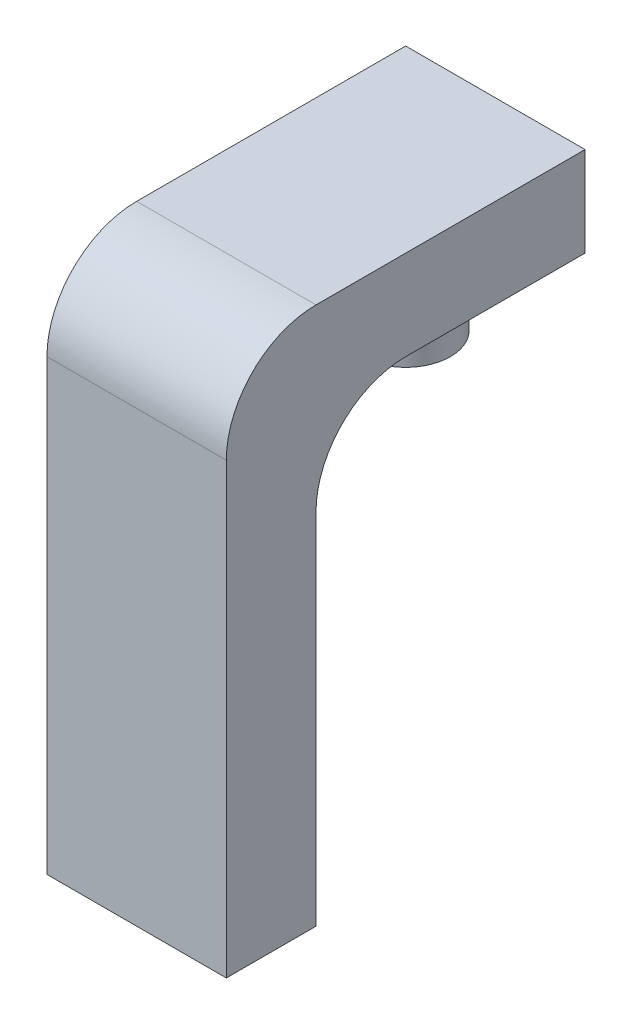
SolidWorks part; units mm, degrees
ref_plane "Alzado" through (0, 0, 0) normal (0, 0, 1) x (1, 0, 0)
ref_plane "Planta" through (0, 0, 0) normal (0, 1, 0) x (1, 0, 0)
ref_plane "Vista lateral" through (0, 0, 0) normal (1, 0, 0) x (0, 0, -1)
sketch "Croquis1" plane through (0, 0, 0) normal (1, 0, 0) x (0, 0, -1)
  line L0 (0, 0) -> (25.4, 0)
  line L1 (0, 0) -> (0, 127)
  line L2 (25.4, 152.4) -> (101.6, 152.4)
  line L3 (101.6, 152.4) -> (101.6, 127)
  line L4 (101.6, 127) -> (50.8, 127)
  line L5 (25.4, 101.6) -> (25.4, 0)
  arc A0 (0, 127) -> (25.4, 152.4) centre (25.4, 127) cw
  arc A1 (50.8, 127) -> (25.4, 101.6) centre (50.8, 101.6) ccw
  dimension "D1" = 25.4
  dimension "D2" = 25.4
  dimension "D3" = 127
  dimension "D4" = 101.6
  dimension "D5" = 76.2
extrude "Saliente-Extruir1" add sketch "Croquis1" along normal blind 50.8
sketch "Croquis2" plane through (0, 127, 0) normal (0, -1, 0) x (1, 0, 0)
  line L0 (25.4, -50.8) -> (25.4, -101.6) construction
  line L1 (50.8, -50.8) -> (0, -50.8) construction
  line L2 (50.8, -101.6) -> (0, -101.6) construction
  line L3 (0, -76.2) -> (50.8, -76.2) construction
  line L4 (0, -50.8) -> (0, -101.6) construction
  line L5 (50.8, -50.8) -> (50.8, -101.6) construction
  circle A0 centre (25.4, -76.2) radius 12.7
  dimension "D1" = 25.4
extrude "Saliente-Extruir2" add sketch "Croquis2" along normal blind 19.05
ref_plane "Plano1" through (25.4, 0, 0) normal (-1, 0, 0) x (0, 0, 1)
